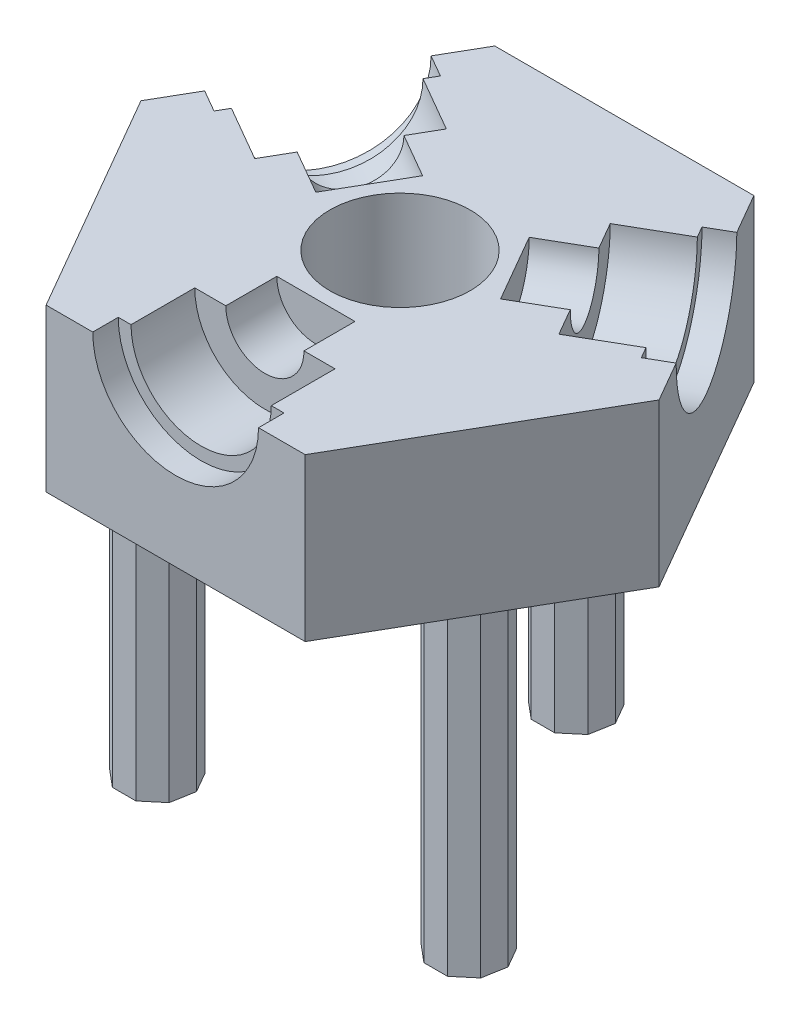
SolidWorks part; units mm, degrees
ref_plane "Front Plane" through (0, 0, 0) normal (0, 0, 1) x (1, 0, 0)
ref_plane "Top Plane" through (0, 0, 0) normal (0, 1, 0) x (1, 0, 0)
ref_plane "Right Plane" through (0, 0, 0) normal (1, 0, 0) x (0, 0, -1)
sketch "Sketch1" plane through (0, 0, 0) normal (0, 1, 0) x (1, 0, 0)
  line L1 (10.16, -17.5976) -> (20.32, 0)
  line L2 (20.32, 0) -> (10.16, 17.5976)
  line L3 (10.16, 17.5976) -> (-10.16, 17.5976)
  line L4 (-10.16, 17.5976) -> (-20.32, 0)
  line L5 (-20.32, 0) -> (-10.16, -17.5976)
  line L6 (-10.16, -17.5976) -> (10.16, -17.5976)
  circle A0 centre (0, 0) radius 17.5976 construction
  dimension "D1" = 20.32
extrude "Boss-Extrude1" add sketch "Sketch1" along normal blind 12.7 contours L4 L5 L6 L1 L2 L3
sketch "Sketch2" plane through (0, 0, 0) normal (0, -1, 0) x (1, 0, 0)
  circle A0 centre (0, 0) radius 5.5
  circle A1 centre (0, 0) radius 8
  dimension "D1" = 11
  dimension "D2" = 16
extrude "Boss-Extrude2" add sketch "Sketch2" along normal blind 3.5
sketch "Sketch5" plane through (0, 12.7, 0) normal (0, 1, 0) x (1, 0, 0)
  line L14 (0, -17.5976) -> (0, -6.5976)
  line L15 (-10.16, -17.5976) -> (10.16, -17.5976) construction
  line L16 (0, -6.5976) -> (-3.0653, -6.5976)
  line L17 (-3.0653, -6.5976) -> (-3.0653, -10.5976)
  line L18 (-3.0653, -10.5976) -> (-5.5, -10.5976)
  line L19 (-5.5, -10.5976) -> (-5.5, -15.5976)
  line L20 (-5.5, -15.5976) -> (-6.5, -15.5976)
  line L21 (-6.5, -15.5976) -> (-6.5, -17.5976)
  line L22 (-6.5, -17.5976) -> (0, -17.5976)
  dimension "D1" = 6.5
  dimension "D2" = 5.5
  dimension "D3" = 2
  dimension "D4" = 5
  dimension "D5" = 4
  dimension "D6" = 3.0653
revolve "Cut-Revolve1" cut sketch "Sketch5" angle 360 about L14
pattern_circular "CirPattern1" count 3 over 360 about axis through (0, 0, 0) along (0, 1, 0) of "Cut-Revolve1"
sketch "Sketch6" plane through (0, 12.7, 0) normal (0, 1, 0) x (1, 0, 0)
  circle A0 centre (0, 0) radius 5.5
  dimension "D1" = 11
extrude "Cut-Extrude1" cut sketch "Sketch6" against normal through all
sketch "Random Circles" plane through (0, 12.7, 0) normal (0, 1, 0) x (1, 0, 0)
  line L0 (10.16, 17.5976) -> (-10.16, 17.5976) construction
  line L1 (-20.32, 0) -> (-10.16, -17.5976) construction
  line L2 (10.16, -17.5976) -> (20.32, 0) construction
  circle A0 centre (0, 13.0976) radius 1.5
  circle A1 centre (11.3429, -6.5488) radius 1.5
  circle A2 centre (-11.3429, -6.5488) radius 1.5
  point P11 (0, 0)
  dimension "D1" = 3
  dimension "D2" = 3
  dimension "D4" = 3
  dimension "D5" = 3
  dimension "D3" = 3
sketch "Sketch8" plane through (0, 0, 0) normal (0, 1, 0) x (1, 0, 0)
  line L19 (-1.9152, 16.001) -> (-2.8397, 14.3997)
  line L20 (-2.8397, 14.3997) -> (-2.5187, 12.5788)
  line L21 (-2.5187, 12.5788) -> (-1.1023, 11.3903)
  line L22 (-1.1023, 11.3903) -> (0.7467, 11.3903)
  line L23 (0.7467, 11.3903) -> (2.1631, 12.5788)
  line L24 (2.1631, 12.5788) -> (2.4842, 14.3997)
  line L25 (2.4842, 14.3997) -> (1.5597, 16.001)
  line L26 (1.5597, 16.001) -> (-0.1778, 16.6333)
  line L27 (-0.1778, 16.6333) -> (-1.9152, 16.001)
  line L28 (14.8143, -6.3421) -> (13.8899, -4.7409)
  line L29 (13.8899, -4.7409) -> (12.1524, -4.1085)
  line L30 (12.1524, -4.1085) -> (10.4149, -4.7409)
  line L31 (10.4149, -4.7409) -> (9.4905, -6.3421)
  line L32 (9.4905, -6.3421) -> (9.8115, -8.163)
  line L33 (9.8115, -8.163) -> (11.2279, -9.3515)
  line L34 (11.2279, -9.3515) -> (13.0769, -9.3515)
  line L35 (13.0769, -9.3515) -> (14.4933, -8.163)
  line L36 (14.4933, -8.163) -> (14.8143, -6.3421)
  line L37 (-12.9001, -9.6588) -> (-11.0512, -9.6588)
  line L38 (-11.0512, -9.6588) -> (-9.6348, -8.4703)
  line L39 (-9.6348, -8.4703) -> (-9.3137, -6.6495)
  line L40 (-9.3137, -6.6495) -> (-10.2382, -5.0482)
  line L41 (-10.2382, -5.0482) -> (-11.9756, -4.4158)
  line L42 (-11.9756, -4.4158) -> (-13.7131, -5.0482)
  line L43 (-13.7131, -5.0482) -> (-14.6376, -6.6495)
  line L44 (-14.6376, -6.6495) -> (-14.3165, -8.4703)
  line L45 (-14.3165, -8.4703) -> (-12.9001, -9.6588)
  line L48 (10.16, 17.5976) -> (-10.16, 17.5976) construction
  line L49 (-20.32, 0) -> (-10.16, -17.5976) construction
  circle A0 centre (12.1524, -6.8115) radius 2.54 construction
  circle A1 centre (-11.9756, -7.1188) radius 2.54 construction
  circle A2 centre (-0.1778, 13.9303) radius 2.54 construction
  point P3 (0, 0)
  point P4 (0, 0)
  point P37 (-0.0003, 0)
  point P38 (0, 0)
  point P39 (0, 0)
  point P40 (0, 0)
  point P42 (0, 0)
  point P43 (0, 0)
  dimension "D1" = 13.9315
  dimension "D2" = 3
  dimension "D6" = 5.08
  dimension "D3" = 0.9643
  dimension "D4" = 0.964
  dimension "D5" = 13.9315
extrude "Boss-Extrude3" add sketch "Sketch8" against normal blind 25.4
